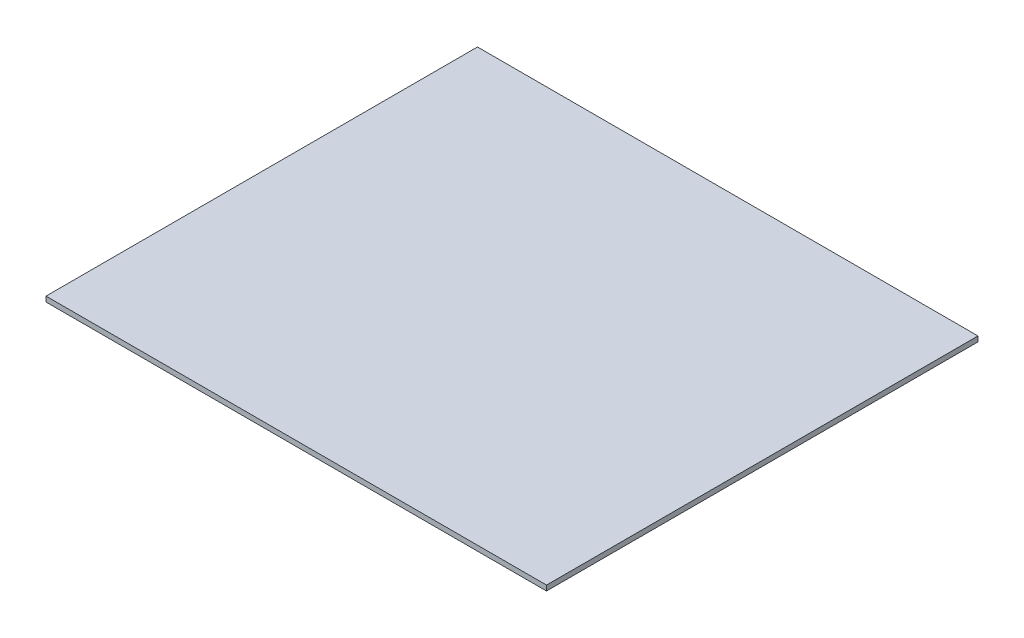
SolidWorks part; units mm, degrees
ref_plane "Piano frontale" through (0, 0, 0) normal (0, 0, 1) x (1, 0, 0)
ref_plane "Piano superiore" through (0, 0, 0) normal (0, 1, 0) x (1, 0, 0)
ref_plane "Piano destro" through (0, 0, 0) normal (1, 0, 0) x (0, 0, -1)
sketch "Schizzo1" plane through (0, -199.1259, 0) normal (0, -1, 0) x (1, 0, 0)
  line L0 (1026.7941, 533.9602) -> (1026.7941, 541.9602) construction
  line L1 (1286.6373, 541.9602) -> (1286.6373, 533.9602) construction
  line L2 (1026.7941, 533.9602) -> (1026.7941, 541.9602) construction
  line L3 (1286.6373, 541.9602) -> (1286.6373, 533.9602) construction
  line L4 (1026.7941, 533.9602) -> (1286.6373, 541.9602) construction
  line L5 (1063.9907, 771.3602) -> (1037.9907, 771.3602) construction
  line L6 (866.7157, 331.3602) -> (1446.7157, 331.3602)
  line L7 (866.7157, 331.3602) -> (866.7157, 831.3602)
  line L8 (866.7157, 831.3602) -> (1446.7157, 831.3602)
  line L9 (1446.7157, 331.3602) -> (1446.7157, 831.3602)
  line L10 (866.7157, 331.3602) -> (1446.7157, 831.3602) construction
  line L11 (866.7157, 831.3602) -> (1446.7157, 331.3602) construction
  line L12 (1156.7157, 537.9602) -> (1156.7157, 581.3602)
  point P10 (1050.9907, 771.3602)
  dimension "D1" = 500
  dimension "D2" = 580
  dimension "D3" = 60
extrude "Estrusione-Estrusione1" add sketch "Schizzo1" along normal blind 6
